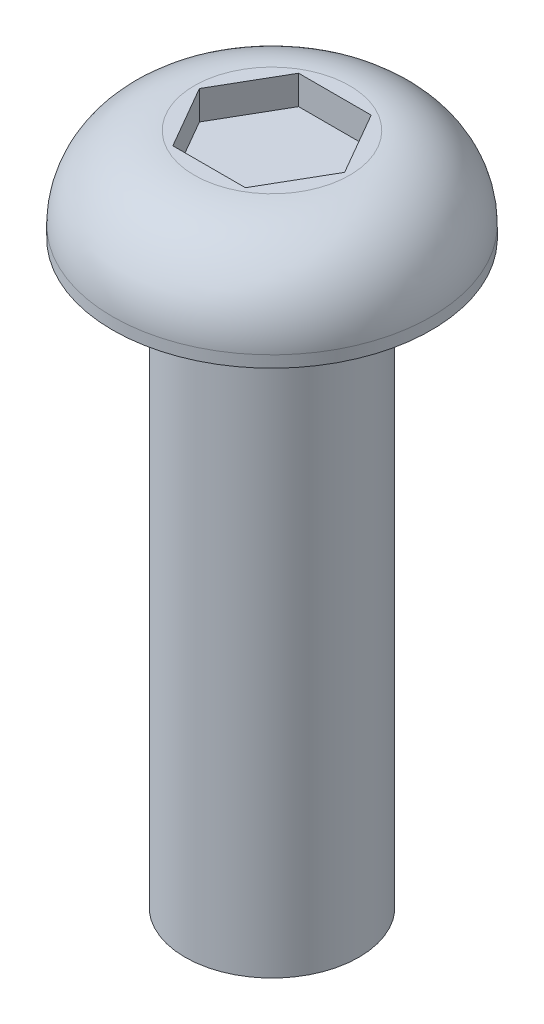
SolidWorks part; units mm, degrees
ref_plane "Front Plane" through (0, 0, 0) normal (0, 0, 1) x (1, 0, 0)
ref_plane "Top Plane" through (0, 0, 0) normal (0, 1, 0) x (1, 0, 0)
ref_plane "Right Plane" through (0, 0, 0) normal (1, 0, 0) x (0, 0, -1)
sketch "Sketch1" plane through (0, 0, 0) normal (0, 0, 1) x (1, 0, 0)
  line L0 (0, 9.0838) -> (0, 0) construction
  line L1 (0, 1.61) -> (1.34, 1.61)
  line L2 (2.75, 0.2) -> (2.75, 0)
  line L3 (2.75, 0) -> (1.5, 0)
  line L4 (1.5, 0) -> (1.5, -10)
  line L5 (1.5, -10) -> (0, -10)
  line L6 (0, 1.61) -> (0, -10)
  arc A0 (1.34, 1.61) -> (2.75, 0.2) centre (1.34, 0.2) cw
  dimension "D1" = 3
  dimension "D2" = 5.5
  dimension "D3" = 1.61
  dimension "D4" = 0.2
  dimension "D5" = 10
revolve "Revolve1" add sketch "Sketch1" angle 360 about L0
sketch "Sketch2" plane through (0, 1.61, 0) normal (0, 1, 0) x (1, 0, 0)
  line L1 (0.6265, 1.0852) -> (-0.6265, 1.0852)
  line L2 (-0.6265, 1.0852) -> (-1.2531, 0)
  line L3 (-1.2531, 0) -> (-0.6265, -1.0852)
  line L4 (-0.6265, -1.0852) -> (0.6265, -1.0852)
  line L5 (0.6265, -1.0852) -> (1.2531, 0)
  line L6 (1.2531, 0) -> (0.6265, 1.0852)
  circle A0 centre (0, 0) radius 1.0852 construction
extrude "Cut-Extrude1" cut sketch "Sketch2" against normal blind 0.5
